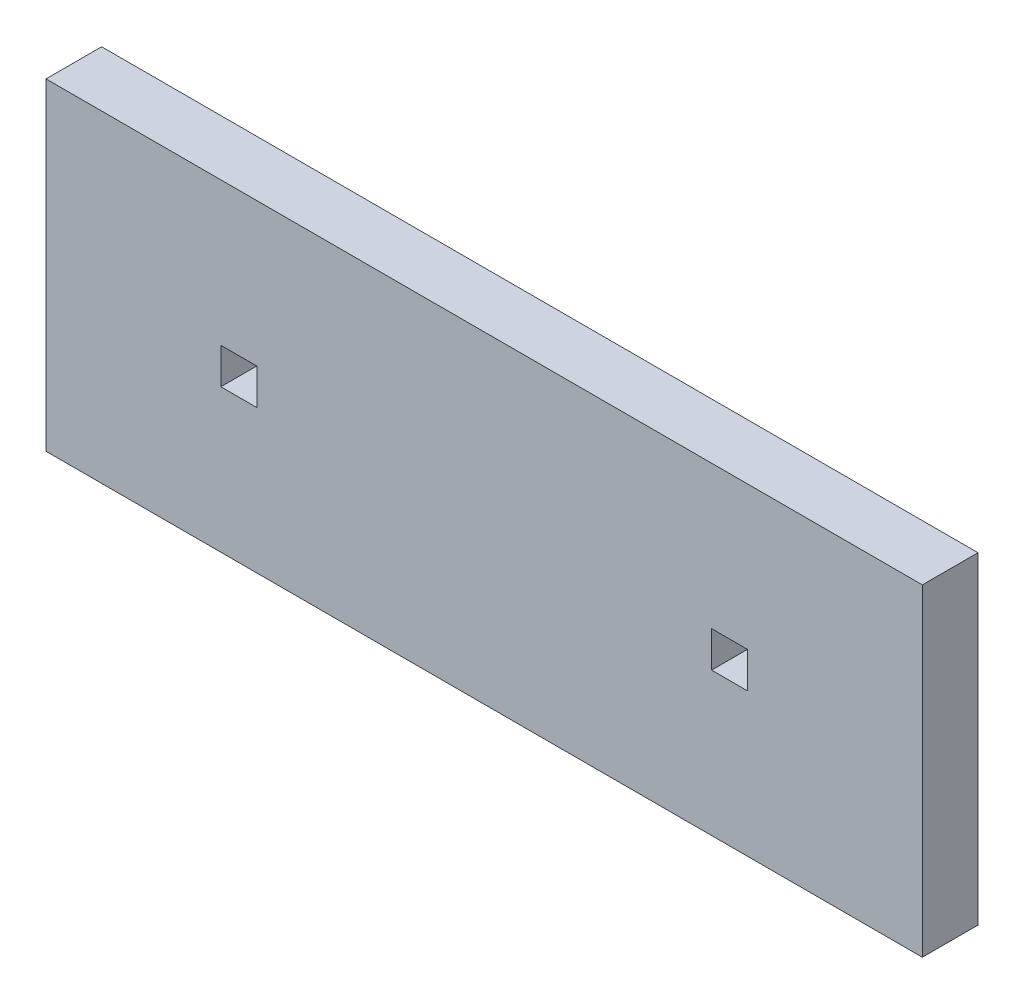
SolidWorks part; units mm, degrees
material "Acrylic (Medium-high impact)"
ref_plane "Front Plane" through (0, 0, 0) normal (0, 0, 1) x (1, 0, 0)
ref_plane "Top Plane" through (0, 0, 0) normal (0, 1, 0) x (1, 0, 0)
ref_plane "Right Plane" through (0, 0, 0) normal (1, 0, 0) x (0, 0, -1)
sketch "Sketch2" plane through (0, 0, 0) normal (0, 0, 1) x (1, 0, 0)
  line L0 (-12.975, -1.5875) -> (12.975, -1.5875) construction
  line L1 (25, -10.7875) -> (-25, -10.7875)
  line L2 (25, -10.7875) -> (25, 10.7875)
  line L3 (25, 10.7875) -> (-25, 10.7875)
  line L4 (-25, -10.7875) -> (-25, 10.7875)
  line L5 (25, -10.7875) -> (-25, 10.7875) construction
  line L6 (25, 10.7875) -> (-25, -10.7875) construction
  line L7 (-15.025, -0.5625) -> (-12.975, -0.5625)
  line L8 (-15.025, -0.5625) -> (-15.025, -2.6125)
  line L9 (-15.025, -2.6125) -> (-12.975, -2.6125)
  line L10 (-12.975, -0.5625) -> (-12.975, -2.6125)
  line L11 (15.025, -2.6125) -> (12.975, -2.6125)
  line L12 (15.025, -2.6125) -> (15.025, -0.5625)
  line L13 (15.025, -0.5625) -> (12.975, -0.5625)
  line L14 (12.975, -2.6125) -> (12.975, -0.5625)
  line L15 (-18, 10.7875) -> (-18, -10.7875) construction
  line L16 (0, -1.6485) -> (0, 1.6485) construction
  line L17 (22.5, 10.7875) -> (20.5, 10.7875)
  line L22 (-25, 10.7875) -> (-18, 10.7875)
  line L23 (-25, 10.7875) -> (-25, 7.6125)
  line L24 (-25, 7.6125) -> (-18, 7.6125)
  line L25 (-18, 10.7875) -> (-18, 7.6125)
  line L26 (-22.5, 7.6125) -> (-20.5, 7.6125)
  line L27 (-22.5, 7.6125) -> (-22.5, 10.7875)
  line L28 (-22.5, 10.7875) -> (-20.5, 10.7875)
  line L29 (-20.5, 7.6125) -> (-20.5, 10.7875)
  line L30 (20.5, 7.6125) -> (20.5, 10.7875)
  line L31 (22.5, 7.6125) -> (20.5, 7.6125)
  line L32 (22.5, 7.6125) -> (22.5, 10.7875)
  line L33 (25, 7.6125) -> (18, 7.6125)
  line L34 (18, 10.7875) -> (18, 7.6125)
  line L35 (25, 10.7875) -> (18, 10.7875)
  line L36 (25, 10.7875) -> (25, 7.6125)
  line L42 (-18, 10.7875) -> (18, 10.7875)
  line L43 (-18, 10.7875) -> (-18, 7.6125)
  line L44 (-18, 7.6125) -> (18, 7.6125)
  line L45 (18, 10.7875) -> (18, 7.6125)
  line L46 (-25, -1) -> (-28.175, -1)
  line L47 (-25, -1) -> (-25, 1)
  line L48 (-25, 1) -> (-28.175, 1)
  line L49 (-28.175, -1) -> (-28.175, 1)
  line L50 (25, -1) -> (28.175, -1)
  line L51 (25, -1) -> (25, 1)
  line L52 (25, 1) -> (28.175, 1)
  line L53 (28.175, -1) -> (28.175, 1)
  point P0 (0, 0)
  point P16 (0, -1.5875)
  point P29 (-21.5, 7.6125)
  point P30 (-21.5, 7.6125)
  point P32 (-22.5, 9.2)
  point P40 (-14, -0.5625)
  point P41 (14, -0.5625)
  point P42 (-15.025, -1.5875)
  point P49 (28.175, 0)
  point P50 (-28.175, 0)
  dimension "D1" = 2.05
  dimension "D3" = 50
  dimension "D6" = 7
  dimension "D7" = 2
  dimension "D8" = 3.175
  dimension "D4" = 28
  dimension "D5" = 9.2
  dimension "D9" = 2
  dimension "D10" = 3.175
  dimension "D2" = 18.4
extrude "Boss-Extrude1" add sketch "Sketch2" along normal blind 3.175 contours L34 L3 L25 L24 L4 L1 L2 L33 L31 L7 L10 L9 L8 L11 L14 L13 L12
equation "\"bottomThickness\"= .220in"
equation "\"wallThickness\"= .125in"
equation "\"D10@Sketch2\"=\"wallThickness\""
equation "\"D8@Sketch2\"=\"wallThickness\""
equation "\"D1@Boss-Extrude1\"=\"wallThickness\""
